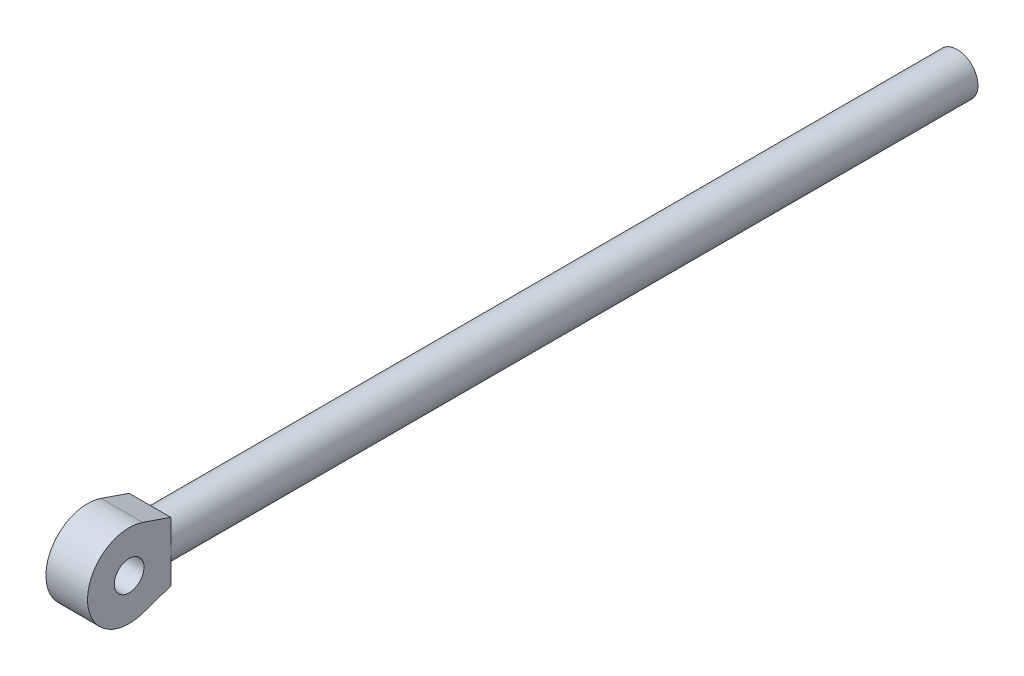
SolidWorks part; units mm, degrees
ref_plane "Front Plane" through (0, 0, 0) normal (0, 0, 1) x (1, 0, 0)
ref_plane "Top Plane" through (0, 0, 0) normal (0, 1, 0) x (1, 0, 0)
ref_plane "Right Plane" through (0, 0, 0) normal (1, 0, 0) x (0, 0, -1)
sketch "Sketch1" plane through (0, 0, 0) normal (0, 0, 1) x (1, 0, 0)
  circle A0 centre (0, 0) radius 17.5
  dimension "D1" = 35
extrude "Boss-Extrude1" add sketch "Sketch1" along normal blind 679
sketch "Sketch3" plane through (0, 0, 0) normal (1, 0, 0) x (0, 0, -1)
  line L0 (-679, 0) -> (-749, 0)
  line L1 (-679, 17.5) -> (-679, -17.5) construction
  line L2 (-679, 0) -> (-679, 25)
  line L3 (-679, 25) -> (-702.6486, 33.1081)
  arc A0 (-702.6486, 33.1081) -> (-749, 0) centre (-714, 0) ccw
  dimension "D1" = 35
  dimension "D2" = 70
  dimension "D3" = 25
extrude "Boss-Extrude3" add sketch "Sketch3" along normal mid plane 35
mirror "Mirror3" about plane through (17.5, 0, 679) normal (0, 1, 0) of "Boss-Extrude3"
sketch "Sketch5" plane through (17.5, 0, 0) normal (1, 0, 0) x (0, 0, -1)
  circle A0 centre (-714, 0) radius 12.5
  dimension "D1" = 25
extrude "Cut-Extrude1" cut sketch "Sketch5" against normal blind 35 contours A0
